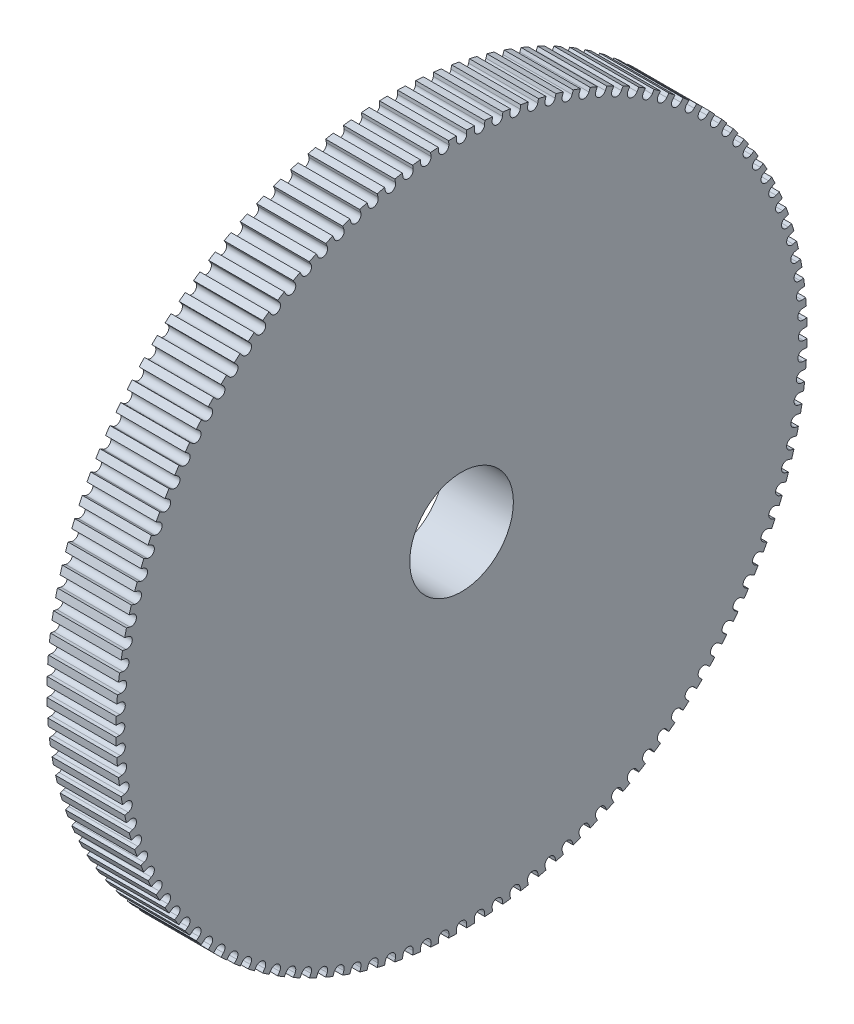
SolidWorks part; units mm, degrees
material "PA Type 6"
ref_plane "Front Plane" through (0, 0, 0) normal (0, 0, 1) x (1, 0, 0)
ref_plane "Top Plane" through (0, 0, 0) normal (0, 1, 0) x (1, 0, 0)
ref_plane "Right Plane" through (0, 0, 0) normal (1, 0, 0) x (0, 0, -1)
sketch "Sketch1" plane through (0, 0, 0) normal (1, 0, 0) x (0, 0, -1)
  circle A0 centre (0, 0) radius 6
  circle A1 centre (0, 0) radius 40
extrude "Boss-Extrude1" add sketch "Sketch1" along normal blind 8
sketch "Sketch2" plane through (8, 0, 0) normal (1, 0, 0) x (0, 0, -1)
  line L0 (0, 47.3535) -> (0, 39.5837) construction
  line L1 (0.6, 47.3535) -> (0.6, 39.5837)
  line L2 (-0.6, 47.3535) -> (-0.6, 39.5837)
  arc A0 (0.6, 47.3535) -> (-0.6, 47.3535) centre (0, 47.3535) ccw
  arc A1 (-0.6, 39.5837) -> (0.6, 39.5837) centre (0, 39.5837) ccw
  point P2 (0, 43.4686)
  point P7 (-0.8364, 47.3535)
  point P8 (0, 39.5837)
  dimension "D1" = 0.6
extrude "Cut-Extrude1" cut sketch "Sketch2" against normal blind 10
pattern_circular "CirPattern1" count 120 over 360 about axis through (0, 0, 0) along (1, 0, 0) of "Cut-Extrude1"
